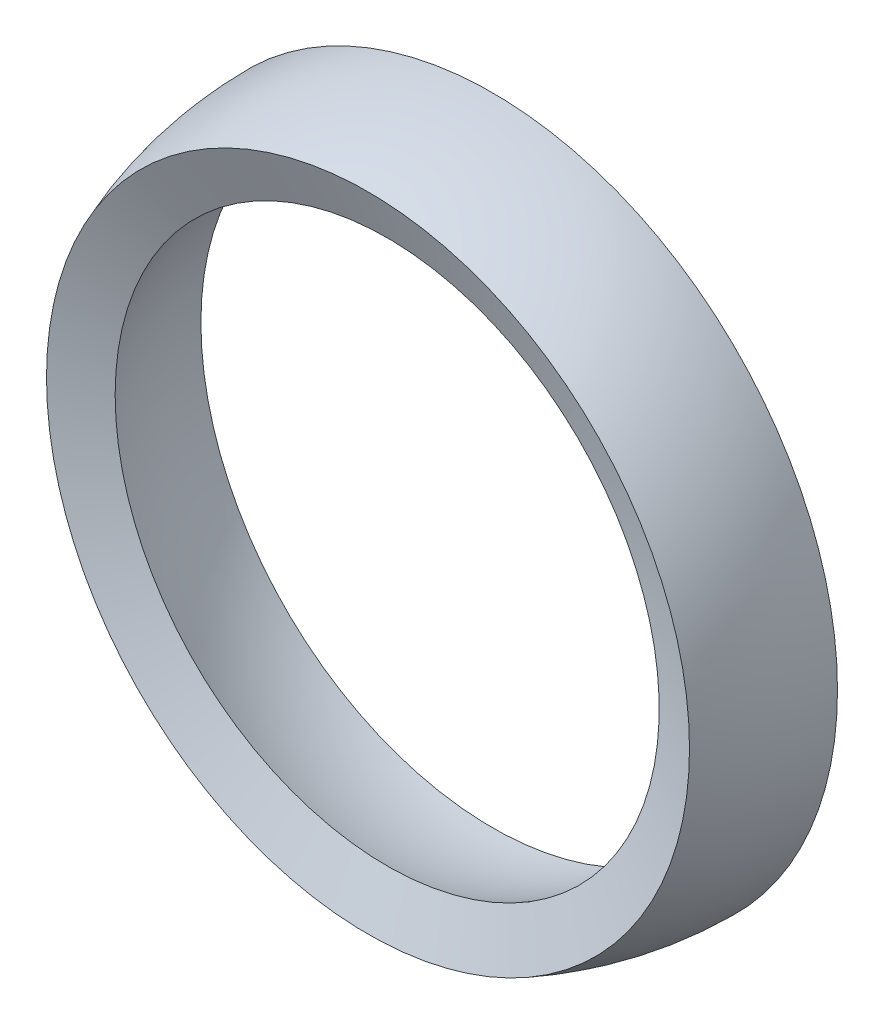
SolidWorks part; units mm, degrees
ref_plane "Front Plane" through (0, 0, 0) normal (0, 0, 1) x (1, 0, 0)
ref_plane "Top Plane" through (0, 0, 0) normal (0, 1, 0) x (1, 0, 0)
ref_plane "Right Plane" through (0, 0, 0) normal (1, 0, 0) x (0, 0, -1)
sketch "Sketch6" plane through (0, 0, 0) normal (0, 1, 0) x (1, 0, 0)
  line L2 (-22, 0) -> (-26, 0)
  line L4 (-24.2413, -9.3998) -> (-20.5119, -7.9537)
  line L5 (-26, 0) -> (-22, 0) construction
  line L7 (0, 0) -> (0, -12.2552) construction
  line L8 (0, 0.4755) -> (0, 0) construction
  line L9 (0, 0) -> (-22, 0) construction
  arc A0 (-22, 0) -> (-20.5119, -7.9537) centre (0, 0) ccw
  arc A1 (-26, 0) -> (-24.2413, -9.3998) centre (0, 0) ccw
  dimension "D2" = 4
  dimension "D1" = 22
revolve "Revolve3" add sketch "Sketch6" angle 360 about L7
